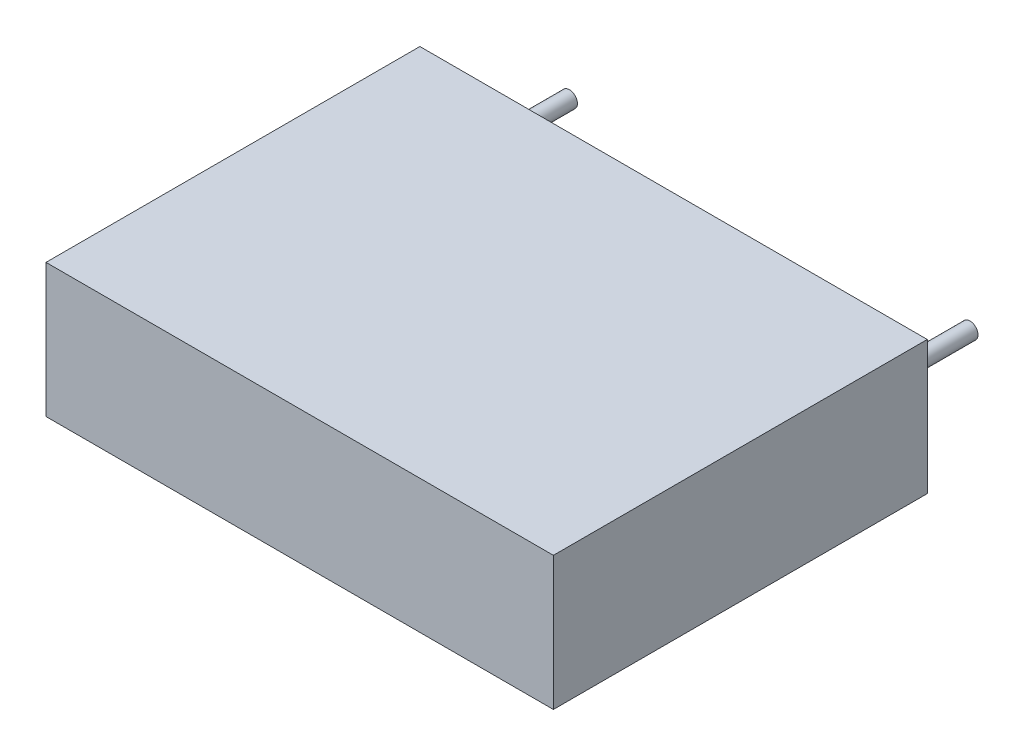
SolidWorks part; units mm, degrees
ref_plane "Plan de face" through (0, 0, 0) normal (0, 0, 1) x (1, 0, 0)
ref_plane "Plan de dessus" through (0, 0, 0) normal (0, 1, 0) x (1, 0, 0)
ref_plane "Plan de droite" through (0, 0, 0) normal (1, 0, 0) x (0, 0, -1)
sketch "Esquisse1" plane through (0, 0, 0) normal (0, 0, 1) x (1, 0, 0)
  line L1 (-9.5, -2.5) -> (9.5, -2.5)
  line L2 (-9.5, -2.5) -> (-9.5, 2.5)
  line L3 (-9.5, 2.5) -> (9.5, 2.5)
  line L4 (9.5, -2.5) -> (9.5, 2.5)
  line L5 (-9.5, -2.5) -> (9.5, 2.5) construction
  line L6 (-9.5, 2.5) -> (9.5, -2.5) construction
  point P0 (0, 0)
  dimension "D1" = 5
  dimension "D2" = 19
extrude "Boss.-Extru.1" add sketch "Esquisse1" along normal blind 14
sketch "Esquisse2" plane through (0, 0, 0) normal (0, 0, -1) x (-1, 0, 0)
  line L0 (-7.5, 0) -> (0, 0) construction
  line L1 (0, 0) -> (7.5, 0) construction
  circle A0 centre (-7.5, 0) radius 0.3
  circle A1 centre (7.5, 0) radius 0.3
  dimension "D1" = 0.6
  dimension "D2" = 15
extrude "Boss.-Extru.2" add sketch "Esquisse2" along normal blind 3.6
